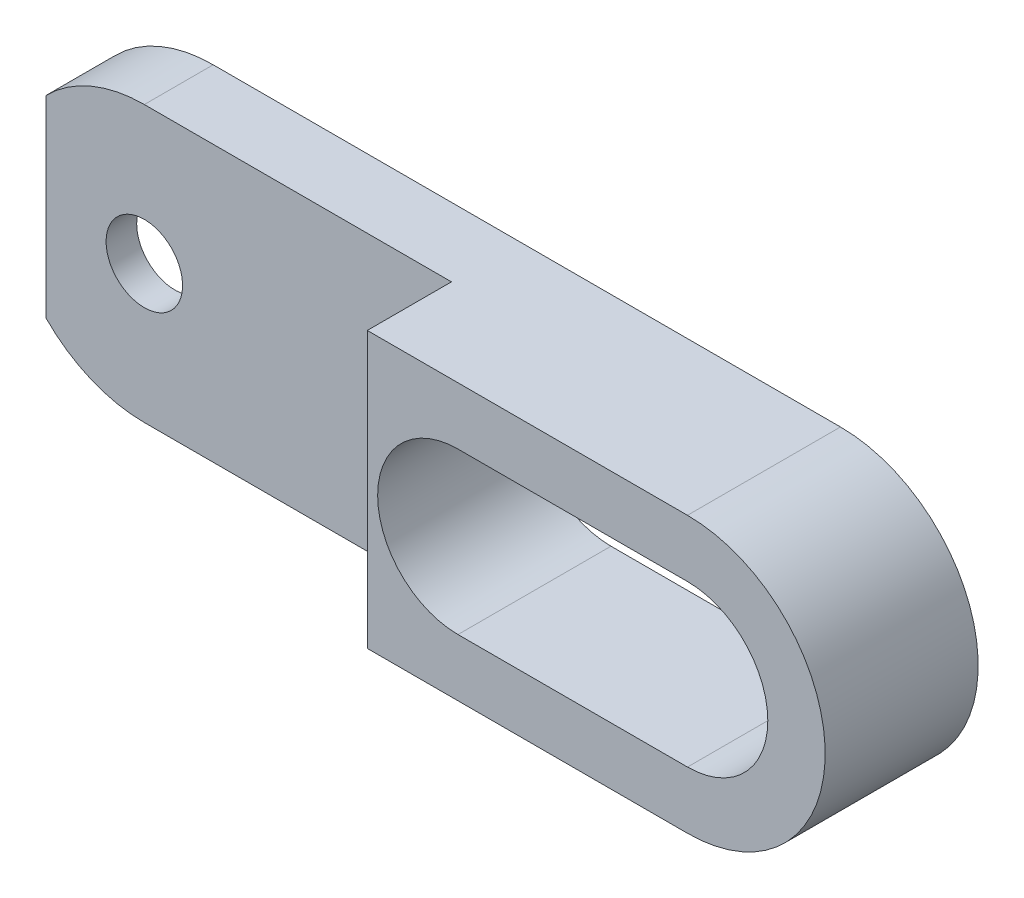
SolidWorks part; units mm, degrees
ref_plane "Front Plane" through (0, 0, 0) normal (0, 0, 1) x (1, 0, 0)
ref_plane "Top Plane" through (0, 0, 0) normal (0, 1, 0) x (1, 0, 0)
ref_plane "Right Plane" through (0, 0, 0) normal (1, 0, 0) x (0, 0, -1)
sketch "Esquisse1" plane through (0, 0, 0) normal (0, 0, 1) x (1, 0, 0)
  line L0 (-4.3758, 4.25) -> (-6.4265, 6.3008)
  line L1 (4.3758, 4.25) -> (17.3156, 2.7822)
  line L2 (17.3156, -2.7822) -> (4.3758, -4.25)
  line L3 (26, 5.25) -> (41, 5.25)
  line L4 (0, 9) -> (41, 9)
  line L5 (0, -9) -> (41, -9)
  line L6 (-4.3758, -4.25) -> (-6.4265, -6.3008)
  line L7 (26, -5.25) -> (41, -5.25)
  arc A0 (4.3758, 4.25) -> (-4.3758, 4.25) centre (0, 0) ccw
  arc A1 (17.3156, -2.7822) -> (17.3156, 2.7822) centre (17, 0) ccw
  arc A2 (4.3758, -4.25) -> (-4.3758, -4.25) centre (0, 0) cw
  arc A3 (-6.4265, 6.3008) -> (0, 9) centre (0, 0) cw
  arc A4 (41, 5.25) -> (41, -5.25) centre (41, 0) cw
  arc A5 (-6.4265, -6.3008) -> (0, -9) centre (0, 0) ccw
  arc A6 (41, 9) -> (41, -9) centre (41, 0) cw
  arc A7 (26, 5.25) -> (26, -5.25) centre (26, 0) ccw
  dimension "D2" = 6.1
  dimension "D3" = 2.8
  dimension "D5" = 5.25
  dimension "D6" = 9
  dimension "D8" = 15
  dimension "D1" = 8.5
  dimension "D4" = 17
  dimension "D7" = 26
extrude "Main" add sketch "Esquisse1" along normal blind 10
sketch "Sketch1" plane through (0, 0, 10) normal (0, 0, 1) x (1, 0, 0)
  line L0 (41, 9) -> (0, 9) construction
  line L1 (20.0735, 9) -> (-6.4265, 9)
  line L2 (20.0735, 9) -> (20.0735, -9)
  line L3 (20.0735, -9) -> (-6.4265, -9)
  line L4 (-6.4265, 9) -> (-6.4265, -9)
  line L6 (0, -9) -> (41, -9) construction
  dimension "D1" = 26.5
extrude "Cut-Extrude1" cut sketch "Sketch1" against normal blind 7.5
sketch "Esquisse2" plane through (0, 0, 2.5) normal (0, 0, -1) x (-1, 0, 0)
  line L0 (0, -9) -> (-20.0735, -9)
  line L1 (0, -9) -> (-41, -9) construction
  line L2 (4.3758, 4.25) -> (6.4265, 6.3008) construction
  line L3 (0, 9) -> (-20.0735, 9)
  line L4 (6.4265, -6.3008) -> (6.4265, 6.3008)
  line L5 (-41, 9) -> (-20.0735, 9) construction
  line L6 (-41, 9) -> (-20.0735, 9) construction
  line L7 (-20.0735, -9) -> (-41, -9) construction
  line L8 (-20.0735, -9) -> (-20.0735, 9) construction
  line L9 (-20.0735, 9) -> (-20.0735, -9)
  arc A1 (0, -9) -> (6.4265, -6.3008) centre (0, 0) ccw
  circle A2 centre (0, 0) radius 2.5
  arc A3 (6.4265, 6.3008) -> (0, 9) centre (0, 0) ccw
  arc A6 (0, -9) -> (6.4265, -6.3008) centre (0, 0) ccw construction
  dimension "D1" = 5
extrude "Boss-Extrude1" add sketch "Esquisse2" against normal blind 2
